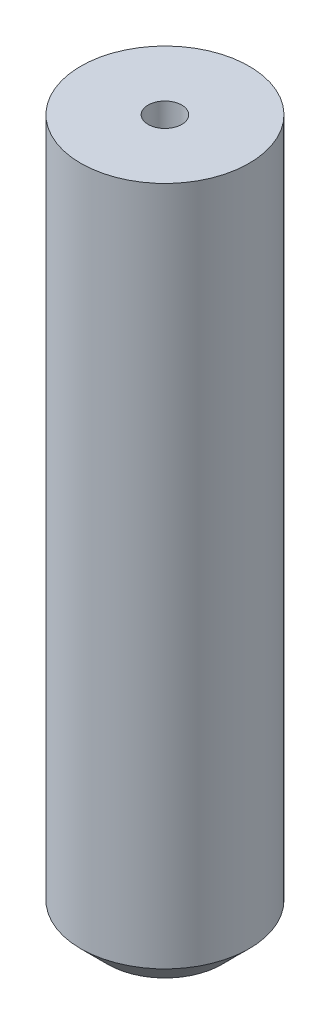
SolidWorks part; units mm, degrees
ref_plane "Front Plane" through (0, 0, 0) normal (0, 0, 1) x (1, 0, 0)
ref_plane "Top Plane" through (0, 0, 0) normal (0, 1, 0) x (1, 0, 0)
ref_plane "Right Plane" through (0, 0, 0) normal (1, 0, 0) x (0, 0, -1)
sketch "Sketch1" plane through (0, 0, 0) normal (0, 1, 0) x (1, 0, 0)
  circle A0 centre (0, 0) radius 12.5
extrude "Boss-Extrude1" add sketch "Sketch1" along normal blind 105
sketch "Sketch2" plane through (0, 105, 0) normal (0, 1, 0) x (1, 0, 0)
  circle A0 centre (0, 0) radius 2.5
extrude "Cut-Extrude1" cut sketch "Sketch2" against normal blind 105
chamfer "Chamfer1" distance 4 angle 45 1 edges at (0, 0, 12.5)
